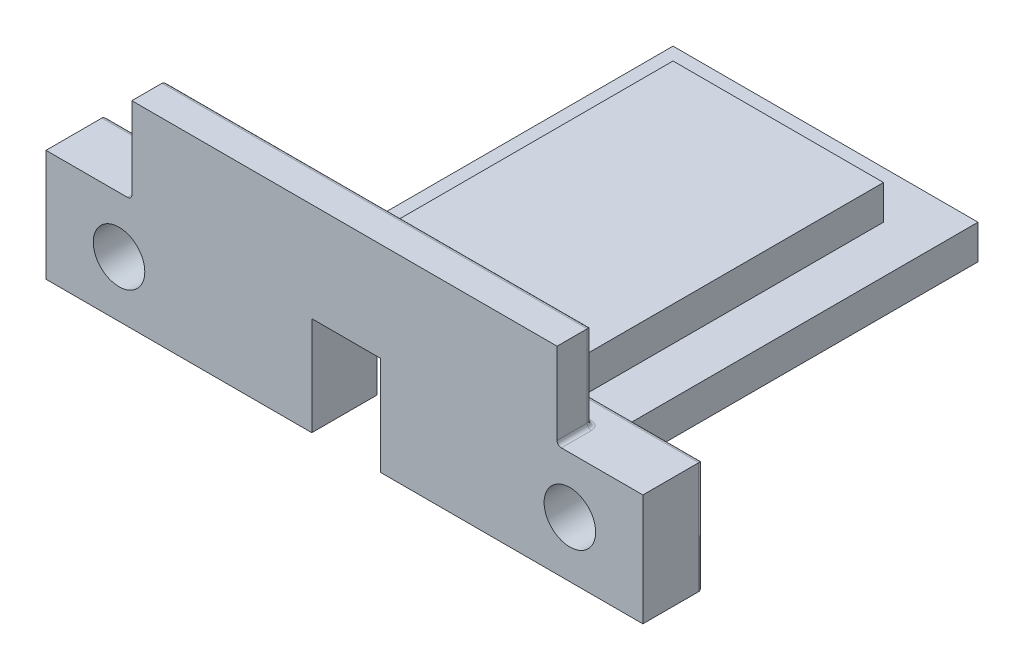
SolidWorks part; units mm, degrees
material "Alliage 1060"
ref_plane "Plan de dessus" through (0, 0, 0) normal (0, 0, 1) x (1, 0, 0)
ref_plane "Plan de droite" through (0, 0, 0) normal (0, 1, 0) x (1, 0, 0)
ref_plane "Plan de face" through (0, 0, 0) normal (1, 0, 0) x (0, 0, -1)
sketch "Esquisse1" plane through (0, 0, 0) normal (0, 1, 0) x (1, 0, 0)
  line L10 (-16.1, -20.9) -> (4, -20.9)
  line L15 (4, -20.9) -> (4, 20)
  line L20 (4, 20) -> (-16.1, 20)
  line L21 (-16.1, 20) -> (-16.1, -20.9)
  line L23 (-24, -28.5) -> (11.5, -28.5)
  line L25 (11.5, -28.5) -> (11.5, 27.5)
  line L26 (11.5, 27.5) -> (-24, 27.5)
  line L27 (-24, -28.5) -> (-24, 27.5)
  dimension "D1" = 4
  dimension "D2" = 11.5
  dimension "D3" = 16.1
  dimension "D4" = 24
  dimension "D5" = 20
  dimension "D6" = 27.5
  dimension "D7" = 20.9
  dimension "D8" = 28.5
extrude "Boss.-Extru.1" add sketch "Esquisse1" along normal blind 4
sketch "Esquisse5" plane through (0, 0, 28.5) normal (0, 0, 1) x (1, 0, 0)
  line L0 (-6.25, 4) -> (-6.25, 21.5906) construction
  line L3 (-6.25, 8) -> (-6.25, 4)
  line L8 (4.5, 4) -> (4.5, 0) construction
  line L9 (-17, 0) -> (4.5, 0) construction
  line L13 (-6.25, 18) -> (-6.25, 8)
  line L14 (18.5, 18) -> (18.5, 13)
  line L22 (-6.25, 18) -> (-6.25, 23)
  line L23 (-6.25, 23) -> (18.5, 23)
  line L24 (18.5, 23) -> (18.5, 18)
  line L25 (-6.25, 4) -> (-6.25, 0)
  line L26 (-24, 0) -> (11.5, 0) construction
  line L27 (-6.25, 0) -> (11.5, 0)
  line L29 (18.5, 13) -> (11.5, 13)
  line L30 (11.5, 13) -> (11.5, 0)
extrude "Boss.-Extru.2" add sketch "Esquisse5" against normal blind 4
mirror "Symétrie1" about plane through (-6.25, 4, 24.5) normal (-1, 0, 0) of "Boss.-Extru.2"
ref_plane "Plan1" through (0, 4, 0) normal (0, -1, 0) x (-1, 0, 0)
sketch "Esquisse9" plane through (0, 4, 0) normal (0, -1, 0) x (-1, 0, 0)
  line L0 (18.5, -23) -> (18.5, -25.5)
  line L1 (18.5, 20) -> (18.5, 22)
  line L8 (-6, 22) -> (18.5, 22)
  line L9 (18.5, -23) -> (18.5, 22)
  line L10 (18.5, -25.5) -> (-6, -25.5)
  line L13 (-6, 22) -> (-6, -25.5)
  dimension "D1" = 18.5
  dimension "D2" = 6
  dimension "D3" = 20
  dimension "D4" = 22
  dimension "D5" = 23
  dimension "D6" = 25.5
extrude "Boss.-Extru.5" add sketch "Esquisse9" against normal blind 4
ref_plane "Plan2" through (-6.25, 0, 0) normal (1, 0, 0) x (0, 0, -1)
sketch "Esquisse10" plane through (0, 0, 28.5) normal (0, 0, 1) x (1, 0, 0)
  line L0 (28.4909, 13) -> (28.4909, 0)
  line L1 (28.4909, 0) -> (11.4909, 0)
  line L2 (11.4909, 13) -> (28.4909, 13)
  line L5 (11.4909, 13) -> (11.4909, 0)
  line L6 (18.5, 13) -> (18.5, 23) construction
  line L7 (-24, 0) -> (11.5, 0) construction
  dimension "D1" = 17
  dimension "D2" = 13
  dimension "D3" = 9.9909
extrude "Boss.-Extru.6" add sketch "Esquisse10" against normal blind 7
mirror "Symétrie2" about plane through (-6.25, 0, 0) normal (1, 0, 0) of "Boss.-Extru.6"
sketch "Esquisse11" plane through (0, 0, 21.5) normal (0, 0, -1) x (-1, 0, 0)
  line L6 (-11.5, 4) -> (-11.5, 0) construction
  line L7 (-11.4909, 13) -> (-11.4909, 4) construction
  line L13 (-11.5, 4) -> (-11.4909, 4) construction
  circle A3 centre (-19.9909, 6.5) radius 3
  dimension "D1" = 8.5
  dimension "D2" = 6
  dimension "D3" = 2.5
extrude "Enlèv. mat.-Extru.1" cut sketch "Esquisse11" against normal blind 7
mirror "Symétrie3" about plane through (-6.25, 0, 0) normal (1, 0, 0) of "Enlèv. mat.-Extru.1"
fillet "Congé1" radius 0.5 20 edges at (18.5, 13, 26.5) (-31, 13, 26.5) (-21.2455, 4, 24.5) (-18.5, 6, 24.5) (-6.25, 8, 24.5) (6, 6, 24.5) (8.7455, 4, 24.5) (11.4909, 8.5, 24.5) (14.9955, 13, 24.5) (18.5, 18, 24.5) (-6.25, 23, 24.5) (-31, 18, 24.5) (-27.4955, 13, 24.5) (-23.9909, 8.5, 24.5) (-40.9909, 6.5, 21.5) (-32.4955, 0, 21.5) (-32.4909, 13, 21.5) (28.4909, 6.5, 21.5) (19.9909, 13, 21.5) (19.9955, 0, 21.5)
sketch "Esquisse12" plane through (0, 0, 0) normal (0, -1, 0) x (1, 0, 0)
  line L3 (-2.05, 28.5) -> (-2.05, 17.9)
  line L4 (-2.05, 17.9) -> (-10.05, 17.9)
  line L5 (-10.05, 17.9) -> (-10.05, 28.5)
  line L6 (-40.9909, 22) -> (-40.9909, 28.5) construction
  line L11 (-2.05, 28.5) -> (-10.05, 28.5)
  line L12 (-6.25, 28.5) -> (11.5, 28.5) construction
  line L13 (-40.9909, 28.5) -> (28.4909, 28.5) construction
  dimension "D1" = 8
  dimension "D3" = 30.9409
  dimension "D4" = 45.4
extrude "Enlèv. mat.-Extru.2" cut sketch "Esquisse12" against normal blind 11.5
